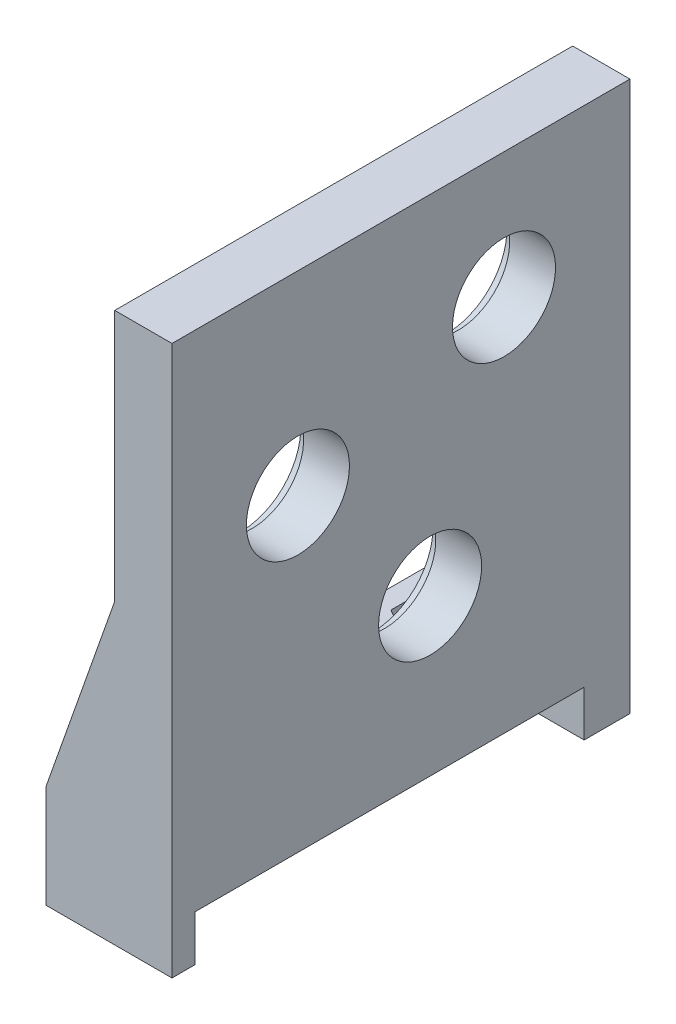
SolidWorks part; units mm, degrees
material "1060 合金"
ref_plane "前视基准面" through (0, 0, 0) normal (0, 0, 1) x (1, 0, 0)
ref_plane "上视基准面" through (0, 0, 0) normal (0, 1, 0) x (1, 0, 0)
ref_plane "右视基准面" through (0, 0, 0) normal (1, 0, 0) x (0, 0, -1)
sketch "草图1" plane through (0, 0, 0) normal (1, 0, 0) x (0, 0, -1)
  line L1 (-11, 17) -> (29, 17)
  line L2 (-11, 17) -> (-11, -27)
  line L3 (-11, -27) -> (29, -27)
  line L4 (29, 17) -> (29, -27)
  circle A6 centre (0, 0) radius 4.5
  circle A7 centre (18, 6) radius 4.5
  circle A8 centre (11.5439, -13.3514) radius 4.5
  dimension "D1" = 20.4
  dimension "D2" = 18.9737
  dimension "D3" = 17.65
  dimension "D4" = 9
  dimension "D5" = 9
  dimension "D7" = 11
  dimension "D6" = 11
  dimension "D8" = 18
  dimension "D9" = 27
  dimension "D10" = 11
extrude "凸台-拉伸1" add sketch "草图1" along normal blind 5
sketch "草图2" plane through (0, 0, 0) normal (-1, 0, 0) x (0, 0, 1)
  circle A0 centre (-18, 6) radius 5.25
  circle A1 centre (0, 0) radius 5.25
  circle A2 centre (-11.5439, -13.3514) radius 5.25
extrude "切除-拉伸1" cut sketch "草图2" against normal blind 1
sketch "草图3" plane through (0, 0, 0) normal (-1, 0, 0) x (0, 0, 1)
  line L0 (11, 17) -> (11, -27) construction
  line L1 (-29, -27) -> (11, -27)
  line L2 (-29, -27) -> (-29, -22)
  line L3 (-29, -22) -> (11, -22)
  line L4 (11, -27) -> (11, -22)
  dimension "D1" = 5
extrude "凸台-拉伸2" add sketch "草图3" along normal blind 6
sketch "草图4" plane through (0, -27, 0) normal (0, -1, 0) x (1, 0, 0)
  line L0 (5, 11) -> (-6, 11)
  line L1 (-6, 11) -> (-6, 9)
  line L2 (-3.8, 9) -> (-0.5, 6)
  line L3 (-6, -29) -> (-6, 11) construction
  line L4 (-0.5, 6) -> (2.8, 9)
  line L5 (-6, 9) -> (-3.8, 9)
  line L6 (5, -29) -> (-4, -29)
  line L7 (5, -29) -> (5, -25)
  line L8 (5, -25) -> (-4, -25)
  line L9 (5, 11) -> (5, -29) construction
  line L10 (5, 9) -> (5, 11)
  line L11 (2.8, 9) -> (5, 9)
  arc A1 (-4, -25) -> (-4, -29) centre (-4, -27) ccw
  dimension "D1" = 5
  dimension "D2" = 2
  dimension "D4" = 4
extrude "凸台-拉伸3" add sketch "草图4" along normal blind 4
sketch "草图5" plane through (0, -27, 0) normal (0, -1, 0) x (1, 0, 0)
  line L0 (5, 9) -> (5, -25) construction
  line L2 (5, -25) -> (-4, -25) construction
  circle A0 centre (-1.5, -19) radius 1.5
  circle A1 centre (-1.5, 1) radius 1.5
  dimension "D3" = 5
  dimension "D4" = 3
  dimension "D5" = 3
  dimension "D6" = 6
  dimension "D1" = 6.5
  dimension "D2" = 6.5
extrude "切除-拉伸2" cut sketch "草图5" against normal blind 5
sketch "草图6" plane through (0, -22, 0) normal (0, 1, 0) x (1, 0, 0)
  line L1 (-1.5, 15.7957) -> (1.275, 17.3979)
  line L2 (1.275, 17.3979) -> (1.275, 20.6021)
  line L3 (1.275, 20.6021) -> (-1.5, 22.2043)
  line L4 (-1.5, 22.2043) -> (-4.275, 20.6021)
  line L5 (-4.275, 20.6021) -> (-4.275, 17.3979)
  line L6 (-4.275, 17.3979) -> (-1.5, 15.7957)
  line L7 (-4.7043, -1) -> (-3.1021, -3.775)
  line L8 (-3.1021, -3.775) -> (0.1021, -3.775)
  line L9 (0.1021, -3.775) -> (1.7043, -1)
  line L10 (1.7043, -1) -> (0.1021, 1.775)
  line L11 (0.1021, 1.775) -> (-3.1021, 1.775)
  line L12 (-3.1021, 1.775) -> (-4.7043, -1)
  circle A0 centre (-1.5, 19) radius 2.775 construction
  circle A1 centre (-1.5, -1) radius 2.775 construction
  dimension "D1" = 5.55
  dimension "D2" = 5.55
extrude "切除-拉伸3" cut sketch "草图6" against normal blind 2.5 and the other way blind 0.5
sketch "草图7" plane through (0, 0, 11) normal (0, 0, 1) x (1, 0, 0)
  line L0 (0, -22) -> (-6, -22)
  line L1 (-6, -22) -> (0, -5)
  line L2 (0, 17) -> (0, -22) construction
  line L3 (0, -5) -> (0, -22)
  dimension "D1" = 17
extrude "凸台-拉伸4" add sketch "草图7" against normal blind 3
sketch "草图8" plane through (0, 0, -29) normal (0, 0, -1) x (-1, 0, 0)
  line L0 (0, -22) -> (6, -22)
  line L1 (6, -22) -> (0, -5)
  line L2 (0, -22) -> (0, 17) construction
  line L3 (0, -5) -> (0, -22)
  dimension "D1" = 17
extrude "凸台-拉伸5" add sketch "草图8" against normal blind 3
